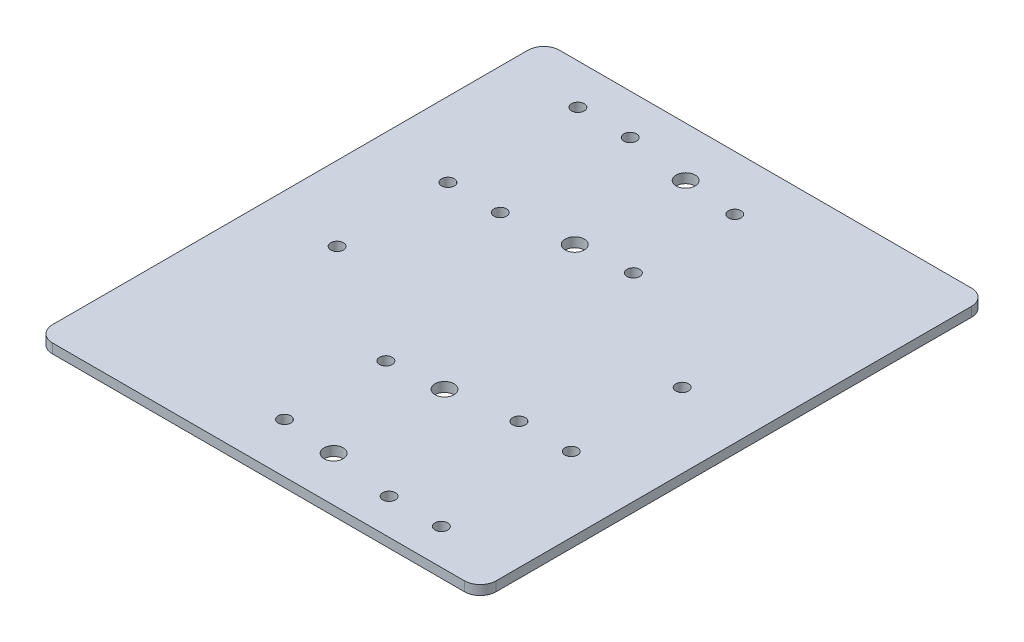
SolidWorks part; units mm, degrees
material "Pine"
ref_plane "Front Plane" through (0, 0, 0) normal (0, 0, 1) x (1, 0, 0)
ref_plane "Top Plane" through (0, 0, 0) normal (0, 1, 0) x (1, 0, 0)
ref_plane "Right Plane" through (0, 0, 0) normal (1, 0, 0) x (0, 0, -1)
sketch "Sketch1" plane through (0, 0, 0) normal (0, 1, 0) x (1, 0, 0)
  line L1 (70, -80) -> (-70, -80)
  line L2 (70, -80) -> (70, 80)
  line L3 (70, 80) -> (-70, 80)
  line L4 (-70, -80) -> (-70, 80)
  line L5 (70, -80) -> (-70, 80) construction
  line L6 (70, 80) -> (-70, -80) construction
  point P0 (0, 0)
  dimension "D1" = 140
  dimension "D2" = 160
extrude "Boss-Extrude1" add sketch "Sketch1" along normal blind 3
ref_plane "Plane1" through (0, 0, -46.8) normal (0, 0, 1) x (1, 0, 0)
ref_plane "Plane4" through (0, 0, 46.8) normal (0, 0, 1) x (1, 0, 0)
sketch "Sketch2" plane through (0, 3, 0) normal (0, 1, 0) x (1, 0, 0)
  line L0 (-1.65, 46.8) -> (1.65, 46.8) construction
  line L1 (-70, 80) -> (-70, -80) construction
  line L2 (70, -80) -> (70, 80) construction
  line L3 (-1.65, -46.8) -> (1.65, -46.8) construction
  line L4 (-70, -80) -> (70, -80) construction
  line L5 (70, 80) -> (-70, 80) construction
  circle A0 centre (-30, 26.3) radius 2
  circle A1 centre (-30, 67.3) radius 2
  circle A2 centre (7.5, 62.8) radius 2
  circle A3 centre (7.5, 30.8) radius 2
  circle A4 centre (30, -68.8) radius 2
  circle A5 centre (-7.5, -64.3) radius 2
  circle A6 centre (30, -27.8) radius 2
  circle A7 centre (-7.5, -32.3) radius 2
  circle A8 centre (46.5, -27.8) radius 2
  circle A9 centre (46.5, -68.8) radius 2
  circle A10 centre (-46.5, 26.3) radius 2
  circle A11 centre (-46.5, 67.3) radius 2
  circle A12 centre (46.5, 7.2) radius 2
  circle A13 centre (-46.5, -8.7) radius 2
  circle A14 centre (9.5, -65.8) radius 3
  circle A15 centre (9.5, -30.8) radius 3
  circle A16 centre (-9.5, 64.3) radius 3
  circle A17 centre (-9.5, 29.3) radius 3
  dimension "D1" = 4
  dimension "D2" = 4
  dimension "D3" = 4
  dimension "D4" = 4
  dimension "D15" = 4
  dimension "D16" = 4
  dimension "D17" = 4
  dimension "D18" = 4
  dimension "D21" = 4
  dimension "D22" = 4
  dimension "D23" = 4
  dimension "D24" = 4
  dimension "D27" = 4
  dimension "D28" = 4
  dimension "D31" = 60.5
  dimension "D34" = 6
  dimension "D35" = 6
  dimension "D36" = 15.7
  dimension "D38" = 6
  dimension "D39" = 6
  dimension "D5" = 32
  dimension "D6" = 41
  dimension "D7" = 20.5
  dimension "D8" = 16
  dimension "D9" = 40
  dimension "D10" = 37.5
  dimension "D11" = 41
  dimension "D12" = 32
  dimension "D13" = 17
  dimension "D14" = 40
  dimension "D19" = 22
  dimension "D20" = 15.7
  dimension "D25" = 16.5
  dimension "D26" = 16.5
  dimension "D29" = 35
  dimension "D30" = 35
  dimension "D32" = 14.2
  dimension "D33" = 35
  dimension "D37" = 60.5
  dimension "D40" = 35
extrude "Cut-Extrude1" cut sketch "Sketch2" against normal through all
fillet "Fillet1" radius 5 4 edges at (-70, 1.5, -80) (70, 1.5, -80) (70, 1.5, 80) (-70, 1.5, 80)
